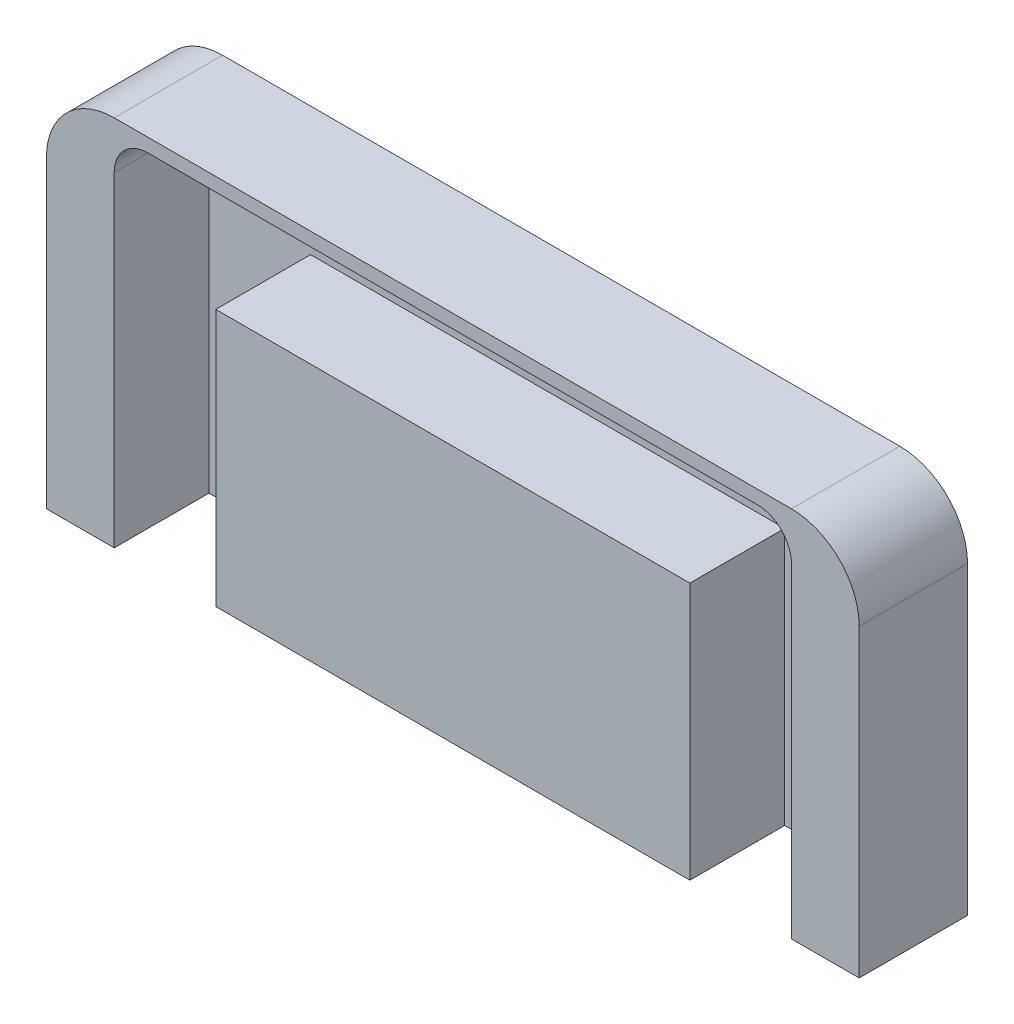
SolidWorks part; units mm, degrees
ref_plane "正面" through (0, 0, 0) normal (0, 0, 1) x (1, 0, 0)
ref_plane "平面" through (0, 0, 0) normal (0, 1, 0) x (1, 0, 0)
ref_plane "右側面" through (0, 0, 0) normal (1, 0, 0) x (0, 0, -1)
sketch "ｽｹｯﾁ1" plane through (0, 0, 0) normal (0, 0, 1) x (1, 0, 0)
  line L1 (-0.6856, 0) -> (23.3144, 0)
  line L2 (-0.6856, 0) -> (-0.6856, 11)
  line L3 (-0.6856, 11) -> (23.3144, 11)
  line L4 (23.3144, 0) -> (23.3144, 11)
  dimension "D1" = 24
  dimension "D2" = 11
extrude "ﾎﾞｽ - 押し出し1" add sketch "ｽｹｯﾁ1" along normal blind 3.2
sketch "ｽｹｯﾁ2" plane through (0, 0, 3.2) normal (0, 0, 1) x (1, 0, 0)
  line L0 (11.3144, 11) -> (11.3144, 0) construction
  line L1 (23.3144, 11) -> (-0.6856, 11) construction
  line L2 (-0.6856, 0) -> (23.3144, 0) construction
  line L3 (-0.6856, 5.5) -> (23.3144, 5.5) construction
  line L4 (-0.6856, 11) -> (-0.6856, 0) construction
  line L5 (23.3144, 0) -> (23.3144, 11) construction
  line L7 (21.3144, 7.6) -> (1.3144, 7.6)
  line L8 (21.3144, 7.6) -> (21.3144, 10.6)
  line L9 (21.3144, 10.6) -> (1.3144, 10.6)
  line L10 (1.3144, 7.6) -> (1.3144, 10.6)
  line L11 (21.3144, 7.6) -> (1.3144, 10.6) construction
  line L12 (21.3144, 10.6) -> (1.3144, 7.6) construction
  point P12 (11.3144, 9.1)
  dimension "D1" = 0.4
  dimension "D2" = 20
  dimension "D3" = 3
extrude "ｶｯﾄ - 押し出し1" cut sketch "ｽｹｯﾁ2" against normal blind 2.8
sketch "ｽｹｯﾁ3" plane through (0, 0, 3.2) normal (0, 0, 1) x (1, 0, 0)
  line L0 (-0.6856, 0) -> (23.3144, 0) construction
  line L1 (21.3144, 7.6) -> (18.3144, 7.6)
  line L2 (21.3144, 7.6) -> (21.3144, 0)
  line L3 (21.3144, 0) -> (18.3144, 0)
  line L4 (18.3144, 7.6) -> (18.3144, 0)
  line L6 (1.3144, 7.6) -> (4.3144, 7.6)
  line L7 (1.3144, 7.6) -> (1.3144, 0)
  line L8 (1.3144, 0) -> (4.3144, 0)
  line L9 (4.3144, 7.6) -> (4.3144, 0)
  dimension "D1" = 3
  dimension "D2" = 3
extrude "ｶｯﾄ - 押し出し2" cut sketch "ｽｹｯﾁ3" against normal blind 2.8
fillet "ﾌｨﾚｯﾄ1" radius 2 2 edges at (23.3144, 11, 1.6) (-0.6856, 11, 1.6)
fillet "ﾌｨﾚｯﾄ2" radius 1 2 edges at (21.3144, 10.6, 1.8) (1.3144, 10.6, 1.8)
